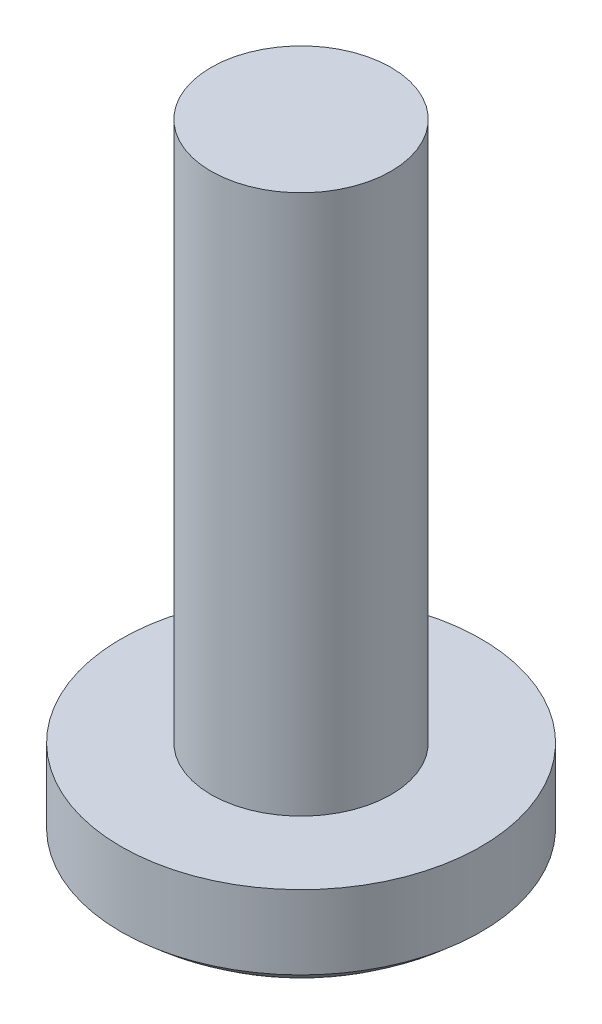
SolidWorks part; units mm, degrees
ref_plane "Front" through (0, 0, 0) normal (0, 0, 1) x (1, 0, 0)
ref_plane "Top" through (0, 0, 0) normal (0, 1, 0) x (1, 0, 0)
ref_plane "Right" through (0, 0, 0) normal (1, 0, 0) x (0, 0, -1)
sketch "草图1" plane through (0, 0, 0) normal (0, 1, 0) x (1, 0, 0)
  circle A0 centre (0, 0) radius 2
  dimension "D1" = 4
extrude "凸台-拉伸1" add sketch "草图1" along normal blind 1.6
sketch "草图2" plane through (0, 1.6, 0) normal (0, 1, 0) x (1, 0, 0)
  circle A0 centre (0, 0) radius 1
  dimension "D1" = 2
extrude "凸台-拉伸2" add sketch "草图2" along normal blind 6
sketch "草图3" plane through (0, 0, 0) normal (1, 0, 0) x (0, 0, -1)
  line L0 (-2, 0.7791) -> (-3.6323, -0.9364)
  line L2 (0, 1.0359) -> (0, -1.9035) construction
  line L3 (-3.6323, -0.9364) -> (3.5435, -0.9364)
  line L4 (3.5435, -0.9364) -> (2, 0.7791)
  line L5 (2, 0) -> (2, 1.6) construction
  line L6 (-2, 1.6) -> (-2, 0) construction
  arc A0 (-2, 0.7791) -> (2, 0.7791) centre (0, 2.9566) ccw
revolve "切除-旋转3" cut sketch "草图3" angle 360 about L2
ref_plane "基准面1" through (0, -5, 0) normal (0, 1, 0) x (1, 0, 0)
sketch "草图4" plane through (0, -5, 0) normal (0, 1, 0) x (1, 0, 0)
  line L0 (-1, 0) -> (1, 0) construction
  line L1 (0, -1) -> (0, 1) construction
  line L2 (-1, -0.2) -> (-0.2, -0.2)
  line L3 (0.2, -1) -> (0.2, -0.2)
  line L4 (-1, 0.2) -> (-0.2, 0.2)
  line L5 (-0.2, -1) -> (-0.2, -0.2)
  line L6 (-1, -0.2) -> (-1, 0.2)
  line L7 (1, -0.2) -> (1, 0.2)
  line L8 (0.2, -1) -> (-0.2, -1)
  line L9 (0.2, 1) -> (-0.2, 1)
  line L10 (0.2, -0.2) -> (1, -0.2)
  line L11 (-0.2, 0.2) -> (-0.2, 1)
  line L12 (-1, -0.2) -> (1, -0.2) construction
  line L13 (0.2, 0.2) -> (1, 0.2)
  line L14 (-0.2, -1) -> (-0.2, 1) construction
  line L15 (0.2, 0.2) -> (0.2, 1)
  line L16 (-1, 0.2) -> (1, 0.2) construction
  line L18 (0.2, -1) -> (0.2, 1) construction
  dimension "D1" = 1
  dimension "D2" = 1
  dimension "D3" = 1
  dimension "D4" = 1
  dimension "D5" = 0.2
  dimension "D6" = 0.2
extrude "切除-拉伸1" cut sketch "草图4" along normal offset from surface (6 mm away) 0.6 up to face at (0, 1.6, 1)
